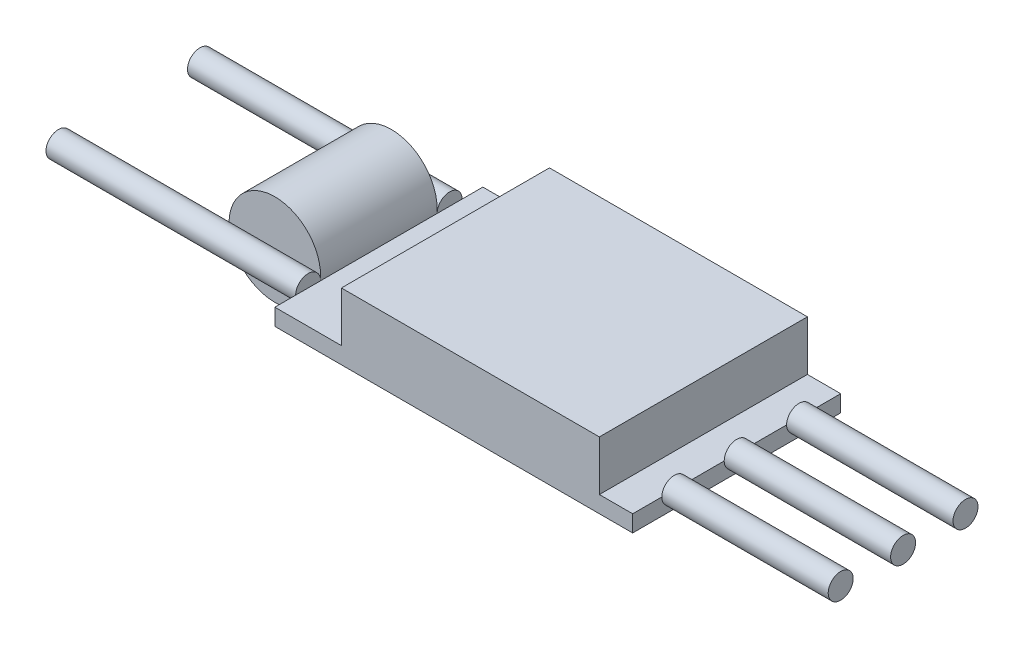
SolidWorks part; units mm, degrees
ref_plane "Front" through (0, 0, 0) normal (0, 0, 1) x (1, 0, 0)
ref_plane "Top" through (0, 0, 0) normal (0, 1, 0) x (1, 0, 0)
ref_plane "Right" through (0, 0, 0) normal (1, 0, 0) x (0, 0, -1)
sketch "Sketch1" plane through (0, 0, 0) normal (0, 1, 0) x (1, 0, 0)
  line L1 (21.5, -12.5) -> (-21.5, -12.5)
  line L2 (21.5, -12.5) -> (21.5, 12.5)
  line L3 (21.5, 12.5) -> (-21.5, 12.5)
  line L4 (-21.5, -12.5) -> (-21.5, 12.5)
  line L5 (21.5, -12.5) -> (-21.5, 12.5) construction
  line L6 (21.5, 12.5) -> (-21.5, -12.5) construction
  point P0 (0, 0)
  dimension "D1" = 43
  dimension "D2" = 25
extrude "Boss-Extrude1" add sketch "Sketch1" along normal blind 2
sketch "Sketch2" plane through (0, 0, 0) normal (0, 0, 1) x (1, 0, 0)
  circle A0 centre (-27, 2.5) radius 5.5
  point P2 (-27, -3)
  point P3 (-27, 8)
  point P5 (-21.5, 2.5)
  dimension "D1" = 11
  dimension "D2" = 3
  dimension "D3" = 6
extrude "Boss-Extrude2" add sketch "Sketch2" along normal mid plane 14 separate body
sketch "Sketch3" plane through (0, 2, 0) normal (0, 1, 0) x (1, 0, 0)
  line L0 (21.5, 12.5) -> (-21.5, 12.5) construction
  line L1 (-13.5, 12.5) -> (17.5, 12.5)
  line L2 (-13.5, 12.5) -> (-13.5, -12.5)
  line L3 (-13.5, -12.5) -> (17.5, -12.5)
  line L4 (17.5, 12.5) -> (17.5, -12.5)
  line L5 (-21.5, -12.5) -> (21.5, -12.5) construction
  line L7 (21.5, -12.5) -> (21.5, 12.5) construction
  line L8 (-21.5, 12.5) -> (-21.5, -12.5) construction
  dimension "D1" = 4
  dimension "D2" = 31
  dimension "D3" = 8
extrude "Boss-Extrude3" add sketch "Sketch3" along normal blind 6
sketch "Sketch4" plane through (-21.5, 0, 0) normal (-1, 0, 0) x (0, 0, 1)
  line L0 (-12.5, 2) -> (12.5, 2) construction
  line L1 (-7, 8) -> (-7, -3) construction
  line L2 (7, -3) -> (7, 8) construction
  circle A0 centre (-8.5, 2) radius 1.5
  circle A1 centre (8.5, 2) radius 1.5
  dimension "D1" = 3
extrude "Boss-Extrude4" add sketch "Sketch4" along normal blind 30
sketch "Sketch5" plane through (21.5, 0, 0) normal (1, 0, 0) x (0, 0, -1)
  line L0 (-12.5, 2) -> (12.5, 2) construction
  line L1 (-12.5, 2) -> (12.5, 2) construction
  line L2 (-7.5, 2) -> (0, 2) construction
  line L3 (0, 2) -> (7.5, 2) construction
  circle A0 centre (-7.5, 2) radius 1.5
  circle A1 centre (0, 2) radius 1.5
  circle A2 centre (7.5, 2) radius 1.5
  dimension "D2" = 3
  dimension "D1" = 5
extrude "Boss-Extrude5" add sketch "Sketch5" along normal blind 20
